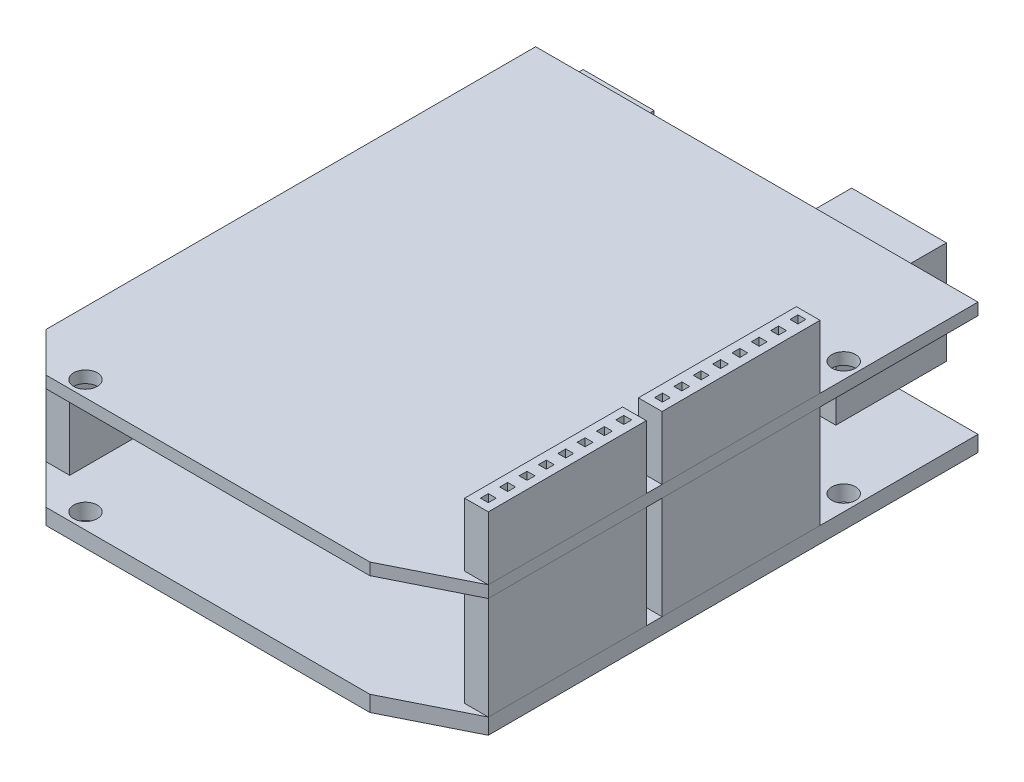
SolidWorks part; units mm, degrees
material "Листовой ламинированный компаунд"
ref_plane "Спереди" through (0, 0, 0) normal (0, 0, 1) x (1, 0, 0)
ref_plane "Сверху" through (0, 0, 0) normal (0, 1, 0) x (1, 0, 0)
ref_plane "Справа" through (0, 0, 0) normal (1, 0, 0) x (0, 0, -1)
sketch "Эскиз1" plane through (0, 0, 0) normal (0, 1, 0) x (1, 0, 0)
  line L0 (0, 33.5) -> (0, -33.5) construction
  line L1 (-28, 33.5) -> (28, 33.5)
  line L2 (-28, 33.5) -> (-28, -28.5)
  line L3 (-23, -33.5) -> (18, -33.5)
  line L4 (28, 33.5) -> (28, -28.5)
  line L5 (-28, 33.5) -> (28, -33.5) construction
  line L6 (-28, -33.5) -> (28, 33.5) construction
  line L7 (-28, -28.5) -> (-23, -33.5)
  line L8 (18, -33.5) -> (28, -28.5)
  circle A0 centre (-20, -31.5) radius 1.5
  circle A1 centre (26, 18.5) radius 1.5
  point P0 (0, 0)
  dimension "D1" = 3
  dimension "D2" = 3
  dimension "D6" = 20
  dimension "D8" = 50
  dimension "D3" = 56
  dimension "D4" = 67
  dimension "D5" = 26
  dimension "D7" = 15
  dimension "D9" = 10
  dimension "D10" = 5
extrude "Бобышка-Вытянуть1" add sketch "Эскиз1" along normal blind 1.5
ref_plane "Плоскость1" through (0, -15, 0) normal (0, 1, 0) x (1, 0, 0)
sketch "Эскиз2" plane through (0, -15, 0) normal (0, 1, 0) x (1, 0, 0)
  line L4 (28, 33.5) -> (-28, 33.5)
  line L5 (28, -28.5) -> (28, 33.5)
  line L6 (-23, -33.5) -> (18, -33.5)
  line L7 (-28, 33.5) -> (-28, -28.5)
  line L8 (28, 33.5) -> (-28, 33.5)
  line L9 (28, -28.5) -> (28, 33.5)
  line L10 (-23, -33.5) -> (18, -33.5)
  line L11 (-28, 33.5) -> (-28, -28.5)
  line L13 (-28, -28.5) -> (-23, -33.5)
  line L14 (-28, -28.5) -> (-23, -33.5)
  line L16 (18, -33.5) -> (28, -28.5)
  line L17 (18, -33.5) -> (28, -28.5)
  circle A1 centre (26, 18.5) radius 1.5
  circle A2 centre (26, 18.5) radius 1.5
  circle A3 centre (-20, -31.5) radius 1.5
  circle A4 centre (-20, -31.5) radius 1.5
  dimension "D1" = 0
  dimension "D2" = 0
  dimension "D3" = 0
extrude "Бобышка-Вытянуть2" add sketch "Эскиз2" along normal blind 2 separate body
sketch "Эскиз3" plane through (0, -13, 0) normal (0, 1, 0) x (1, 0, 0)
  line L0 (25, -6.5) -> (25, 13.5)
  line L1 (28, -28.5) -> (25, -28.5)
  line L2 (28, -28.5) -> (28, -8.5)
  line L3 (28, -8.5) -> (25, -8.5)
  line L4 (25, -28.5) -> (25, -8.5)
  line L5 (28, 13.5) -> (25, 13.5)
  line L6 (28, -6.5) -> (28, 13.5)
  line L7 (28, -6.5) -> (25, -6.5)
  dimension "D1" = 20
  dimension "D2" = 3
  dimension "D3" = 2
extrude "Бобышка-Вытянуть4" add sketch "Эскиз3" along normal up to surface (13 mm away) separate body up to face at (-0.8333, 0, 9.5)
sketch "Эскиз4" plane through (0, 1.5, 0) normal (0, 1, 0) x (1, 0, 0)
  line L0 (25, -8.5) -> (25, -28.5) construction
  line L1 (28, -8.5) -> (25, -8.5) construction
  line L2 (25, -28.5) -> (28, -28.5) construction
  line L3 (25, -8.5) -> (25, -28.5)
  line L4 (28, -8.5) -> (25, -8.5)
  line L5 (25, -28.5) -> (28, -28.5)
  line L6 (28, -28.5) -> (28, -8.5)
  line L7 (25, -6.5) -> (28, -6.5)
  line L8 (25, 13.5) -> (25, -6.5)
  line L9 (28, -6.5) -> (28, 13.5)
  line L10 (28, 13.5) -> (25, 13.5)
  dimension "D1" = 2
extrude "Бобышка-Вытянуть6" add sketch "Эскиз4" along normal blind 8 separate body
sketch "Эскиз5" plane through (0, 9.5, 0) normal (0, 1, 0) x (1, 0, 0)
  line L0 (25, -8.5) -> (25, -28.5) construction
  line L1 (26, -27.5) -> (27, -27.5)
  line L2 (26, -27.5) -> (26, -26.5)
  line L3 (26, -26.5) -> (27, -26.5)
  line L4 (27, -27.5) -> (27, -26.5)
  line L5 (25, -28.5) -> (28, -28.5) construction
  line L6 (26, -25.05) -> (26, -24.05)
  line L7 (26, -24.05) -> (27, -24.05)
  line L8 (27, -25.05) -> (27, -24.05)
  line L9 (26, -25.05) -> (27, -25.05)
  line L10 (26, -22.6) -> (26, -21.6)
  line L11 (26, -21.6) -> (27, -21.6)
  line L12 (27, -22.6) -> (27, -21.6)
  line L13 (26, -22.6) -> (27, -22.6)
  line L14 (26, -20.15) -> (26, -19.15)
  line L15 (26, -19.15) -> (27, -19.15)
  line L16 (27, -20.15) -> (27, -19.15)
  line L17 (26, -20.15) -> (27, -20.15)
  line L18 (26, -17.7) -> (26, -16.7)
  line L19 (26, -16.7) -> (27, -16.7)
  line L20 (27, -17.7) -> (27, -16.7)
  line L21 (26, -17.7) -> (27, -17.7)
  line L22 (26, -15.25) -> (26, -14.25)
  line L23 (26, -14.25) -> (27, -14.25)
  line L24 (27, -15.25) -> (27, -14.25)
  line L25 (26, -15.25) -> (27, -15.25)
  line L26 (26, -12.8) -> (26, -11.8)
  line L27 (26, -11.8) -> (27, -11.8)
  line L28 (27, -12.8) -> (27, -11.8)
  line L29 (26, -12.8) -> (27, -12.8)
  line L30 (26, -10.35) -> (26, -9.35)
  line L31 (26, -9.35) -> (27, -9.35)
  line L32 (27, -10.35) -> (27, -9.35)
  line L33 (26, -10.35) -> (27, -10.35)
  line L38 (26, -5.45) -> (26, -4.45)
  line L39 (26, -4.45) -> (27, -4.45)
  line L40 (27, -5.45) -> (27, -4.45)
  line L41 (26, -5.45) -> (27, -5.45)
  line L42 (26, -3) -> (26, -2)
  line L43 (26, -2) -> (27, -2)
  line L44 (27, -3) -> (27, -2)
  line L45 (26, -3) -> (27, -3)
  line L46 (26, -0.55) -> (26, 0.45)
  line L47 (26, 0.45) -> (27, 0.45)
  line L48 (27, -0.55) -> (27, 0.45)
  line L49 (26, -0.55) -> (27, -0.55)
  line L50 (26, 1.9) -> (26, 2.9)
  line L51 (26, 2.9) -> (27, 2.9)
  line L52 (27, 1.9) -> (27, 2.9)
  line L53 (26, 1.9) -> (27, 1.9)
  line L54 (26, 4.35) -> (26, 5.35)
  line L55 (26, 5.35) -> (27, 5.35)
  line L56 (27, 4.35) -> (27, 5.35)
  line L57 (26, 4.35) -> (27, 4.35)
  line L58 (26, 6.8) -> (26, 7.8)
  line L59 (26, 7.8) -> (27, 7.8)
  line L60 (27, 6.8) -> (27, 7.8)
  line L61 (26, 6.8) -> (27, 6.8)
  line L62 (26, 9.25) -> (26, 10.25)
  line L63 (26, 10.25) -> (27, 10.25)
  line L64 (27, 9.25) -> (27, 10.25)
  line L65 (26, 9.25) -> (27, 9.25)
  line L66 (26, 11.7) -> (26, 12.7)
  line L67 (26, 12.7) -> (27, 12.7)
  line L68 (27, 11.7) -> (27, 12.7)
  line L69 (26, 11.7) -> (27, 11.7)
  line L70 (26, -7.9) -> (26, -6.9) [skipped]
  line L71 (26, -6.9) -> (27, -6.9) [skipped]
  line L72 (27, -7.9) -> (27, -6.9) [skipped]
  line L73 (26, -7.9) -> (27, -7.9) [skipped]
  dimension "D1" = 1
  dimension "D2" = 1
  dimension "D3" = 1
  dimension "D4" = 1
  dimension "D5" = 17
extrude "Вырез-Вытянуть1" cut sketch "Эскиз5" against normal blind 5
sketch "Эскиз6" plane through (0, -13, 0) normal (0, 1, 0) x (1, 0, 0)
  line L0 (-25, -10.5) -> (-25, 5.5)
  line L1 (-28, -28.5) -> (-25, -28.5)
  line L2 (-28, -28.5) -> (-28, -12.5)
  line L3 (-28, -12.5) -> (-25, -12.5)
  line L4 (-25, -28.5) -> (-25, -12.5)
  line L5 (-28, 5.5) -> (-25, 5.5)
  line L6 (-28, -10.5) -> (-28, 5.5)
  line L7 (-28, -10.5) -> (-25, -10.5)
  dimension "D1" = 16
  dimension "D2" = 3
  dimension "D3" = 2
extrude "Бобышка-Вытянуть7" add sketch "Эскиз6" along normal up to surface (13 mm away) separate body up to face at (-0.8333, 0, 9.5)
sketch "Эскиз7" plane through (0, -13, 0) normal (0, 1, 0) x (1, 0, 0)
  line L0 (28, -28.5) -> (28, 33.5) construction
  line L1 (18, 25.5) -> (6, 25.5)
  line L2 (18, 25.5) -> (18, 39.5)
  line L3 (18, 39.5) -> (6, 39.5)
  line L4 (6, 25.5) -> (6, 39.5)
  line L5 (28, 33.5) -> (-28, 33.5) construction
  dimension "D1" = 12
  dimension "D2" = 10
  dimension "D3" = 6
  dimension "D4" = 8
extrude "Бобышка-Вытянуть8" add sketch "Эскиз7" along normal up to surface (13 mm away) separate body up to face at (-0.8333, 0, 9.5)
sketch "Эскиз8" plane through (0, 0, -39.5) normal (0, 0, -1) x (-1, 0, 0)
  line L0 (-16, -11) -> (-8, -11)
  line L1 (-16, -11) -> (-16, -4.2897)
  line L2 (-8, -11) -> (-8, -4.2897)
  line L3 (-18, -13) -> (-6, -13) construction
  line L4 (-6, 0) -> (-6, -13) construction
  line L5 (-18, 0) -> (-18, -13) construction
  arc A0 (-16, -4.2897) -> (-8, -4.2897) centre (-12, -7.2897) cw
  dimension "D4" = 5
  dimension "D1" = 2
  dimension "D2" = 2
  dimension "D3" = 2
extrude "Вырез-Вытянуть2" cut sketch "Эскиз8" against normal blind 10
sketch "Эскиз9" plane through (0, -13, 0) normal (0, 1, 0) x (1, 0, 0)
  line L0 (28, 33.5) -> (-28, 33.5) construction
  line L1 (-15, 23.5) -> (-24, 23.5)
  line L2 (-15, 23.5) -> (-15, 35.5)
  line L3 (-15, 35.5) -> (-24, 35.5)
  line L4 (-24, 23.5) -> (-24, 35.5)
  line L5 (-28, 33.5) -> (-28, -28.5) construction
  dimension "D1" = 9
  dimension "D2" = 2
  dimension "D3" = 4
  dimension "D4" = 10
extrude "Бобышка-Вытянуть9" add sketch "Эскиз9" along normal up to surface (13 mm away) separate body up to face at (-0.8333, 0, 9.5)
sketch "Эскиз10" plane through (0, 0, -35.5) normal (0, 0, -1) x (-1, 0, 0)
  line L0 (24, 0) -> (24, -13) construction
  circle A0 centre (19.5, -6.2221) radius 2.5
  dimension "D1" = 5
  dimension "D2" = 4.5
extrude "Вырез-Вытянуть3" cut sketch "Эскиз10" against normal blind 10
